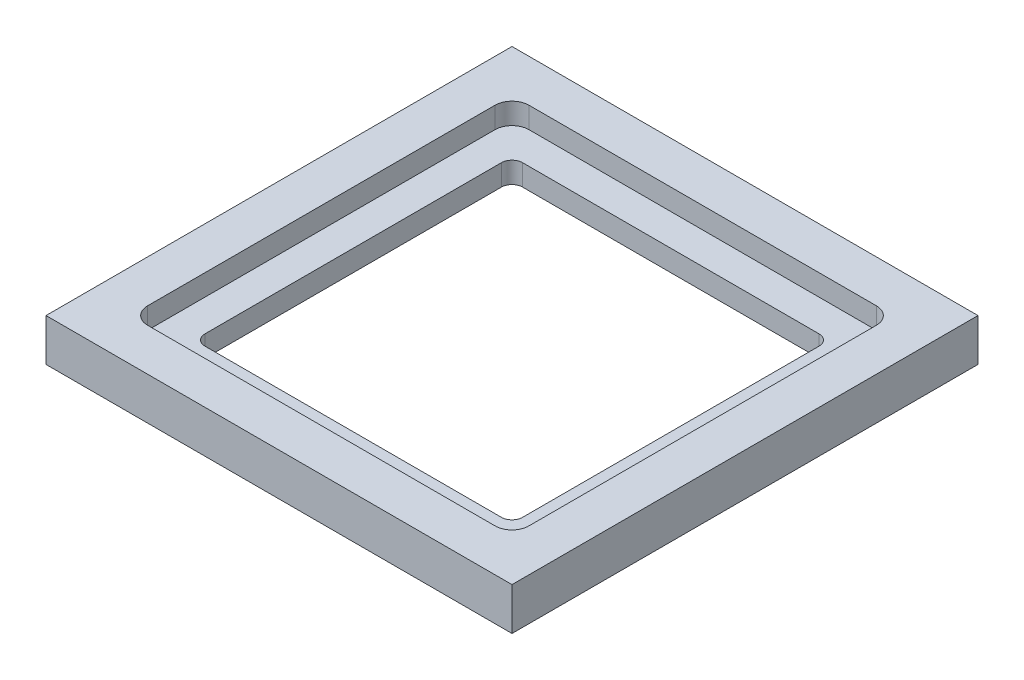
SolidWorks part; units mm, degrees
ref_plane "Front Plane" through (0, 0, 0) normal (0, 0, 1) x (1, 0, 0)
ref_plane "Top Plane" through (0, 0, 0) normal (0, 1, 0) x (1, 0, 0)
ref_plane "Right Plane" through (0, 0, 0) normal (1, 0, 0) x (0, 0, -1)
sketch "Sketch1" plane through (0, 0, 0) normal (0, 1, 0) x (1, 0, 0)
  line L0 (-22, 22) -> (22, 22)
  line L1 (-22, -22) -> (22, -22)
  line L2 (-22, -22) -> (-22, 22)
  line L4 (22, -22) -> (22, 22)
  line L7 (-18, -18) -> (18, -18)
  line L8 (-18, -18) -> (-18, 18)
  line L9 (-18, 18) -> (18, 18)
  line L10 (18, -18) -> (18, 18)
  arc A4 (-17.9676, 18) -> (-18, 17.9893) centre (0, -36.3) ccw
  point P0 (0, 0)
  point P5 (0, 0)
  dimension "D5" = 22
  dimension "D3" = 36
  dimension "D4" = 36
  dimension "D14" = 44
  dimension "D18" = 18
  dimension "D19" = 18
  dimension "D20" = 22
  dimension "D21" = 22
extrude "Boss-Extrude1" add sketch "Sketch1" along normal blind 2
fillet "Fillet1" radius 1.6 4 edges at (-18, 1, 18) (18, 1, 18) (18, 1, -18) (-18, 1, -18)
sketch "Sketch2" plane through (0, 0, 0) normal (0, -1, 0) x (1, 0, 0)
  line L1 (-22, -22) -> (22, -22)
  line L2 (-22, -22) -> (-22, 22)
  line L3 (-22, 22) -> (22, 22)
  line L4 (22, -22) -> (22, 22)
  line L5 (-22, -22) -> (22, 22) construction
  line L6 (-22, 22) -> (22, -22) construction
  line L7 (-15, -15) -> (15, -15)
  line L8 (-15, -15) -> (-15, 15)
  line L9 (-15, 15) -> (15, 15)
  line L10 (15, -15) -> (15, 15)
  line L11 (-15, -15) -> (15, 15) construction
  line L12 (-15, 15) -> (15, -15) construction
  point P0 (0, 0)
  point P5 (0, 0)
  dimension "D1" = 30
extrude "Boss-Extrude2" add sketch "Sketch2" along normal blind 2
fillet "Fillet2" radius 1 4 edges at (-15, -1, 15) (15, -1, 15) (15, -1, -15) (-15, -1, -15)
